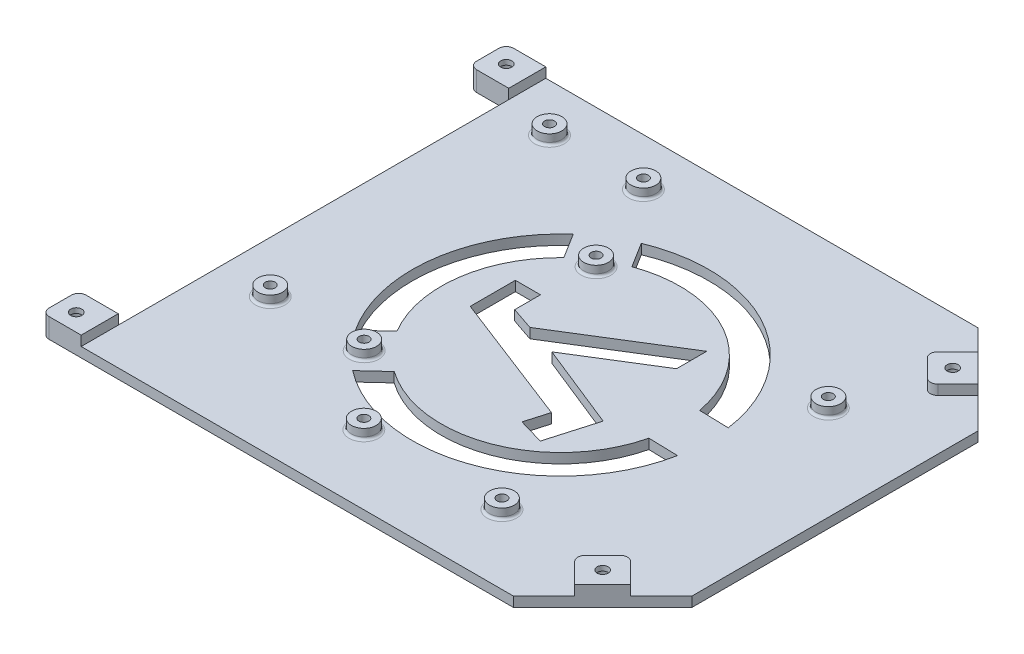
SolidWorks part; units mm, degrees
material "PLA"
ref_plane "Front Plane" through (0, 0, 0) normal (0, 0, 1) x (1, 0, 0)
ref_plane "Top Plane" through (0, 0, 0) normal (0, 1, 0) x (1, 0, 0)
ref_plane "Right Plane" through (0, 0, 0) normal (1, 0, 0) x (0, 0, -1)
sketch "Sketch1" plane through (0, 0, 0) normal (0, 1, 0) x (1, 0, 0)
  line L0 (61.25, 30) -> (44.25, 47)
  line L1 (-44.25, -47) -> (44.25, -47)
  line L3 (-44.25, 47) -> (44.25, 47)
  line L4 (61.25, -30) -> (61.25, 30)
  line L5 (-44.25, -47) -> (44.25, 47) construction
  line L6 (-44.25, 47) -> (44.25, -47) construction
  line L7 (61.25, -30) -> (44.25, -47)
  line L8 (-44.25, 39.5) -> (-44.25, -39.5)
  line L9 (-44.25, 47) -> (-52.25, 47)
  line L11 (-44.25, 39.5) -> (-52.25, 39.5)
  line L12 (-52.25, 47) -> (-52.25, 39.5)
  line L13 (-44.25, -47) -> (-52.25, -47)
  line L15 (-44.25, -39.5) -> (-52.25, -39.5)
  line L16 (-52.25, -47) -> (-52.25, -39.5)
  arc A0 (42.0999, 16.2266) -> (42.0999, 19.4016) centre (42.0999, 17.8141) ccw construction
  arc A1 (42.0999, 19.4016) -> (42.0999, 16.2266) centre (42.0999, 17.8141) ccw construction
  arc A2 (-6.1601, 20.6716) -> (-6.1601, 17.4966) centre (-6.1601, 19.0841) ccw construction
  arc A3 (-6.1601, 17.4966) -> (-6.1601, 20.6716) centre (-6.1601, 19.0841) ccw construction
  arc A4 (26.8599, -34.5734) -> (26.8599, -31.3984) centre (26.8599, -32.9859) ccw construction
  arc A5 (26.8599, -31.3984) -> (26.8599, -34.5734) centre (26.8599, -32.9859) ccw construction
  arc A6 (-1.0801, -34.5734) -> (-1.0801, -31.3984) centre (-1.0801, -32.9859) ccw construction
  arc A7 (-1.0801, -31.3984) -> (-1.0801, -34.5734) centre (-1.0801, -32.9859) ccw construction
  arc A8 (42.0999, 16.2266) -> (42.0999, 19.4016) centre (42.0999, 17.8141) ccw construction
  arc A9 (42.0999, 19.4016) -> (42.0999, 16.2266) centre (42.0999, 17.8141) ccw construction
  arc A10 (-6.1601, 20.6716) -> (-6.1601, 17.4966) centre (-6.1601, 19.0841) ccw construction
  arc A11 (-6.1601, 17.4966) -> (-6.1601, 20.6716) centre (-6.1601, 19.0841) ccw construction
  arc A12 (26.8599, -34.5734) -> (26.8599, -31.3984) centre (26.8599, -32.9859) ccw construction
  arc A13 (26.8599, -31.3984) -> (26.8599, -34.5734) centre (26.8599, -32.9859) ccw construction
  arc A14 (-1.0801, -34.5734) -> (-1.0801, -31.3984) centre (-1.0801, -32.9859) ccw construction
  arc A15 (-1.0801, -31.3984) -> (-1.0801, -34.5734) centre (-1.0801, -32.9859) ccw construction
  point P0 (0, 0)
  point P11 (0, 47)
  point P12 (61.25, 0)
  dimension "D1" = 94
  dimension "D2" = 8
  dimension "D3" = 45
  dimension "D4" = 45
  dimension "D5" = 60
  dimension "D6" = 7.5
  dimension "D7" = 7.5
  dimension "D8" = 105.5
extrude "Boss-Extrude1" add sketch "Sketch1" along normal blind 2
sketch "Sketch2" plane through (0, 2, 0) normal (0, 1, 0) x (1, 0, 0)
  line L0 (-52.25, -47) -> (44.25, -47) construction
  line L1 (-52.25, 47) -> (-44.25, 47)
  line L2 (-52.25, 47) -> (-52.25, 39.5)
  line L3 (-52.25, 39.5) -> (-44.25, 39.5)
  line L4 (-44.25, 47) -> (-44.25, 39.5)
  line L5 (-52.25, -39.5) -> (-44.25, -39.5)
  line L6 (-52.25, -39.5) -> (-52.25, -47)
  line L7 (-52.25, -47) -> (-44.25, -47)
  line L8 (-44.25, -39.5) -> (-44.25, -47)
  line L9 (55.5784, -35.6716) -> (49.9216, -41.3284)
  line L10 (55.5784, -35.6716) -> (49.9216, -30.0147)
  line L11 (49.9216, -41.3284) -> (44.2647, -35.6716)
  line L12 (49.9216, -30.0147) -> (44.2647, -35.6716)
  line L13 (44.25, -47) -> (61.25, -30) construction
  line L14 (61.25, 30) -> (44.25, 47) construction
  line L15 (61.25, 30) -> (44.25, 47) construction
  line L16 (44.25, -47) -> (61.25, -30) construction
  line L17 (49.9216, 41.3284) -> (55.5784, 35.6716)
  line L18 (49.9216, 41.3284) -> (44.2647, 35.6716)
  line L19 (55.5784, 35.6716) -> (49.9216, 30.0147)
  line L20 (44.2647, 35.6716) -> (49.9216, 30.0147)
  line L21 (-52.25, 47) -> (-52.25, 39.5) construction
  line L26 (44.25, 47) -> (-52.25, 47) construction
  line L27 (-44.25, 39.5) -> (-44.25, -39.5) construction
  point P20 (52.75, -38.5)
  point P21 (52.75, -38.5)
  point P23 (52.75, 38.5)
  point P26 (52.75, 38.5)
  dimension "D1" = 8
  dimension "D2" = 8
  dimension "D3" = 8
  dimension "D4" = 8
extrude "Boss-Extrude2" add sketch "Sketch2" along normal blind 2
sketch "Sketch3" plane through (0, 4, 0) normal (0, 1, 0) x (1, 0, 0)
  line L4 (-52.25, -47) -> (-44.25, -47) construction
  line L5 (-52.25, -39.5) -> (-52.25, -47) construction
  line L6 (-44.25, 47) -> (-52.25, 47) construction
  line L7 (-52.25, 47) -> (-52.25, 39.5) construction
  line L8 (0, 0) -> (67.1807, 0) construction
  line L9 (61.25, -30) -> (61.25, 30) construction
  circle A0 centre (49.65, 35.405) radius 1.125
  circle A2 centre (-48.75, -43.5) radius 1.125
  circle A3 centre (-48.75, 43.5) radius 1.125
  circle A4 centre (49.65, -35.405) radius 1.125
  dimension "D1" = 2.25
  dimension "D7" = 2.25
  dimension "D10" = 2.25
  dimension "D2" = 70.81
  dimension "D3" = 11.6
  dimension "D8" = 3.5
  dimension "D9" = 3.5
  dimension "D11" = 3.5
  dimension "D12" = 3.5
extrude "Cut-Extrude1" cut sketch "Sketch3" against normal through all
sketch "Sketch4" plane through (0, 2, 0) normal (0, 1, 0) x (1, 0, 0)
  line L0 (-44.25, 39.5) -> (-44.25, -39.5) construction
  line L1 (44.25, 47) -> (-44.25, 47) construction
  circle A0 centre (-33.9, 37.4) radius 2.5
  circle A1 centre (-14.9, 37.4) radius 2.5
  circle A2 centre (-33.9, -19.1) radius 2.5
  circle A3 centre (-14.9, -19.1) radius 2.5
  circle A4 centre (-6.1601, 19.0841) radius 2.5
  circle A5 centre (42.0999, 17.8141) radius 2.5
  circle A6 centre (-1.0801, -32.9859) radius 2.5
  circle A7 centre (26.8599, -32.9859) radius 2.5
  dimension "D1" = 5
  dimension "D4" = 5
  dimension "D6" = 5
  dimension "D8" = 5
  dimension "D9" = 5
  dimension "D12" = 5
  dimension "D15" = 5
  dimension "D18" = 5
  dimension "D2" = 10.35
  dimension "D3" = 9.6
  dimension "D5" = 19
  dimension "D7" = 56.5
extrude "Boss-Extrude3" add sketch "Sketch4" along normal blind 2
sketch "Sketch5" plane through (0, 4, 0) normal (0, 1, 0) x (1, 0, 0)
  circle A0 centre (-33.9, 37.4) radius 1
  circle A1 centre (-14.9, 37.4) radius 1
  circle A2 centre (-6.1601, 19.0841) radius 1
  circle A3 centre (42.0999, 17.8141) radius 1
  circle A4 centre (26.8599, -32.9859) radius 1
  circle A5 centre (-1.0801, -32.9859) radius 1
  circle A6 centre (-14.9, -19.1) radius 1
  circle A7 centre (-33.9, -19.1) radius 1
  dimension "D1" = 2
  dimension "D2" = 2
  dimension "D3" = 2
  dimension "D4" = 2
  dimension "D5" = 2
  dimension "D6" = 2
  dimension "D7" = 2
  dimension "D8" = 2
extrude "Cut-Extrude2" cut sketch "Sketch5" against normal blind 2.5
fillet "Fillet1" radius 0.5 8 edges at (-1.0801, 2, 30.4859) (26.8599, 2, 30.4859) (42.0999, 2, -20.3141) (-33.9, 2, 16.6) (-14.9, 2, 16.6) (-6.1601, 2, -21.5841) (-14.9, 2, -39.9) (-33.9, 2, -39.9)
sketch "Sketch6" plane through (0, 0, 0) normal (0, -1, 0) x (1, 0, 0)
  line L0 (-44.25, -39.5) -> (-44.25, 39.5) construction
  line L1 (-11.9341, 0.6084) -> (-11.9341, -8.526)
  line L2 (-11.9341, -8.526) -> (-6.8546, -8.526)
  line L3 (-6.8546, -8.526) -> (-6.8546, -3.3185)
  line L4 (-6.8546, -3.3185) -> (-2.202, -1.7392)
  line L5 (-2.202, -1.7392) -> (19.8658, -15.4409)
  line L6 (19.8658, -15.4409) -> (19.8658, -9.337)
  line L7 (19.8658, -9.337) -> (4.3022, 0.3263)
  line L8 (4.3022, 0.3263) -> (21.6159, 7.2672)
  line L9 (21.6159, 7.2672) -> (18.756, 17.1273)
  line L10 (18.756, 17.1273) -> (13.5478, 15.6167)
  line L11 (13.5478, 15.6167) -> (14.8875, 10.9977)
  line L12 (14.8875, 10.9977) -> (-11.9341, 0.6084)
  line L17 (5.75, 0) -> (-35.55, 38.2) construction
  line L21 (5.75, 0) -> (2.7469, -4.812) construction
  line L22 (5.75, 0) -> (42.327, 0.9785) construction
  line L23 (-12.5705, 23.7562) -> (-8.1998, 19.7136)
  line L24 (-19.3607, 16.415) -> (-14.99, 12.3724)
  line L25 (-2.5172, -22.6909) -> (-5.6693, -27.7416)
  line L26 (-11.0007, -17.3965) -> (-14.1528, -22.4472)
  line L27 (-6.6803, -19.9177) -> (-6.1601, -19.0841) construction
  line L28 (29.2346, 5.63) -> (35.1861, 5.7892)
  line L29 (29.502, -4.3664) -> (35.4535, -4.2072)
  arc A0 (-19.3607, 16.415) -> (-14.1528, -22.4472) centre (5.75, 0) ccw
  arc A1 (-14.99, 12.3724) -> (-11.0007, -17.3965) centre (5.75, 0) ccw
  circle A2 centre (-6.1601, -19.0841) radius 1 construction
  circle A3 centre (-14.9, 19.1) radius 1 construction
  circle A4 centre (-6.1601, -19.0841) radius 1 construction
  circle A5 centre (-14.9, 19.1) radius 1 construction
  arc A6 (-2.5172, -22.6909) -> (29.502, -4.3664) centre (5.75, 0) ccw
  arc A7 (-5.6693, -27.7416) -> (35.4535, -4.2072) centre (5.75, 0) ccw
  arc A8 (29.2346, 5.63) -> (-8.1998, 19.7136) centre (5.75, 0) ccw
  arc A9 (35.1861, 5.7892) -> (-12.5705, 23.7562) centre (5.75, 0) ccw
  dimension "D1" = 60
  dimension "D3" = 48.3
  dimension "D2" = 50
  dimension "D5" = 123.5
  dimension "D6" = 5
  dimension "D7" = 5
  dimension "D8" = 5
  dimension "D9" = 5
  dimension "D10" = 5
  dimension "D11" = 5
extrude "Cut-Extrude6" cut sketch "Sketch6" against normal through all
fillet "Fillet2" radius 1.5 4 edges at (-52.25, 2, -47) (-52.25, 2, -39.5) (-52.25, 2, 39.5) (-52.25, 2, 47)
fillet "Fillet3" radius 1.5 4 edges at (49.9216, 3, 30.0147) (44.2647, 3, 35.6716) (49.9216, 3, -30.0147) (44.2647, 3, -35.6716)
sketch "Sketch7" plane through (0, 2, 0) normal (0, 1, 0) x (1, 0, 0)
  line L0 (41.9034, 49.3466) -> (63.964, 27.286)
  line L1 (41.9034, 49.3466) -> (41.3731, 48.8162)
  line L2 (63.964, 27.286) -> (63.4337, 26.7557)
  line L3 (41.3731, 48.8162) -> (63.4337, 26.7557)
  line L4 (61.25, 30) -> (55.5784, 35.6716) construction
  line L5 (41.987, -49.263) -> (64.1624, -27.0876)
  line L6 (41.987, -49.263) -> (41.4567, -48.7327)
  line L7 (64.1624, -27.0876) -> (63.6321, -26.5573)
  line L8 (41.4567, -48.7327) -> (63.6321, -26.5573)
  line L9 (55.5784, -35.6716) -> (61.25, -30) construction
  dimension "D1" = 0.75
  dimension "D2" = 0.75
extrude "Cut-Extrude7" cut sketch "Sketch7" against normal through all both and the other way through all
sketch "Sketch8" plane through (0, 0, 0) normal (0, -1, 0) x (1, 0, 0)
  circle A0 centre (-48.75, 43.5) radius 2
  circle A1 centre (49.65, 35.405) radius 2
  circle A2 centre (49.65, -35.405) radius 2
  circle A3 centre (-48.75, -43.5) radius 2
  dimension "D1" = 4
  dimension "D2" = 4
  dimension "D3" = 4
  dimension "D4" = 4
extrude "Cut-Extrude8" cut sketch "Sketch8" against normal offset from surface 1 and the other way through all up to face at (-48.75, 4, -42.375)
